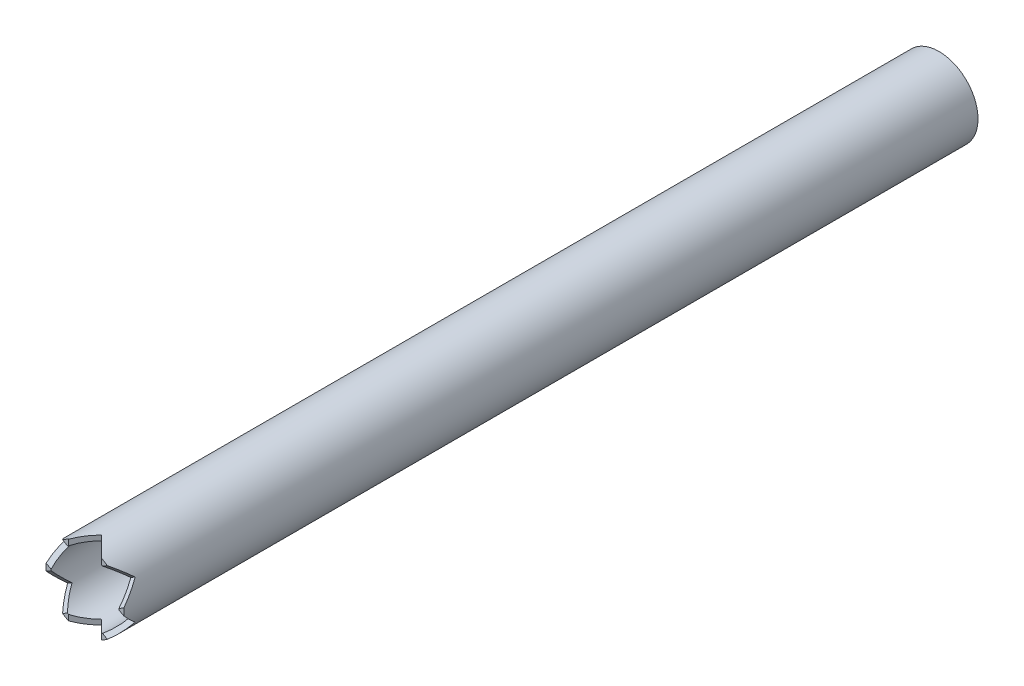
SolidWorks part; units mm, degrees
material "PVC Rigid"
ref_plane "Front Plane" through (0, 0, 0) normal (0, 0, 1) x (1, 0, 0)
ref_plane "Top Plane" through (0, 0, 0) normal (0, 1, 0) x (1, 0, 0)
ref_plane "Right Plane" through (0, 0, 0) normal (1, 0, 0) x (0, 0, -1)
sketch "Sketch1" plane through (0, 0, 0) normal (0, 1, 0) x (1, 0, 0)
  line L0 (0, 0) -> (0, 660.4)
  dimension "D1" = 660.4
other "Pipe (standard, s40) P2(1)"
ref_plane "Plane1" through (0, 0, 0) normal (0, 0, -1) x (-1, 0, 0)
sketch "Sketch12" plane through (0, 0, 0) normal (0, 0, -1) x (-1, 0, 0)
  circle A0 centre (0, 0) radius 26.2509
  circle A1 centre (0, 0) radius 30.1625
  point P3 (0, 0)
  dimension "In_dia" = 52.5018
  dimension "Out_dia" = 60.325
sketch "Sketch13" plane through (0, 0, 0) normal (0, 1, 0) x (1, 0, 0)
  line L0 (0, 660.4) -> (0, 0) construction
sketch "Sketch14" plane through (0, 0, 0) normal (0, 1, 0) x (1, 0, 0)
  line L0 (0, 12.7) -> (-12.7, 0)
  line L1 (0, 0) -> (0, 660.4) construction
  line L2 (-30.1625, 0) -> (30.1625, 0) construction
  line L3 (-12.7, 0) -> (12.7, 0)
  line L4 (12.7, 0) -> (0, 12.7)
  dimension "D1" = 25.4
  dimension "D2" = 12.7
  dimension "D3" = 12.7
extrude "Cut-Extrude1" cut sketch "Sketch14" against normal through all and the other way through all
ref_plane "Plane2" through (0, 0, 0) normal (0.866, -0.5, 0) x (0, 0, -1)
sketch "Sketch15" plane through (0, 0, 0) normal (0.866, -0.5, 0) x (0, 0, -1)
  line L0 (0, 12.7) -> (0, -12.7)
  line L1 (0, 30.1625) -> (0, -17.3431) construction
  line L2 (0, -12.7) -> (12.7, 0)
  line L3 (0, 0) -> (660.4, 0) construction
  line L4 (12.7, 0) -> (0, 12.7)
  dimension "D1" = 25.4
  dimension "D2" = 12.7
  dimension "D3" = 12.7
extrude "Cut-Extrude2" cut sketch "Sketch15" against normal through all and the other way through all
ref_plane "Plane3" through (0, 0, 0) normal (-0.866, -0.5, 0) x (0, 0, -1)
sketch "Sketch16" plane through (0, 0, 0) normal (-0.866, -0.5, 0) x (0, 0, -1)
  line L0 (0, 12.7) -> (0, -12.7)
  line L1 (0, 17.3431) -> (0, -17.3431) construction
  line L2 (0, -12.7) -> (12.7, 0)
  line L3 (0, 0) -> (660.4, 0) construction
  line L4 (12.7, 0) -> (0, 12.7)
  dimension "D1" = 25.4
  dimension "D2" = 12.7
  dimension "D3" = 12.7
extrude "Cut-Extrude3" cut sketch "Sketch16" against normal through all and the other way through all
